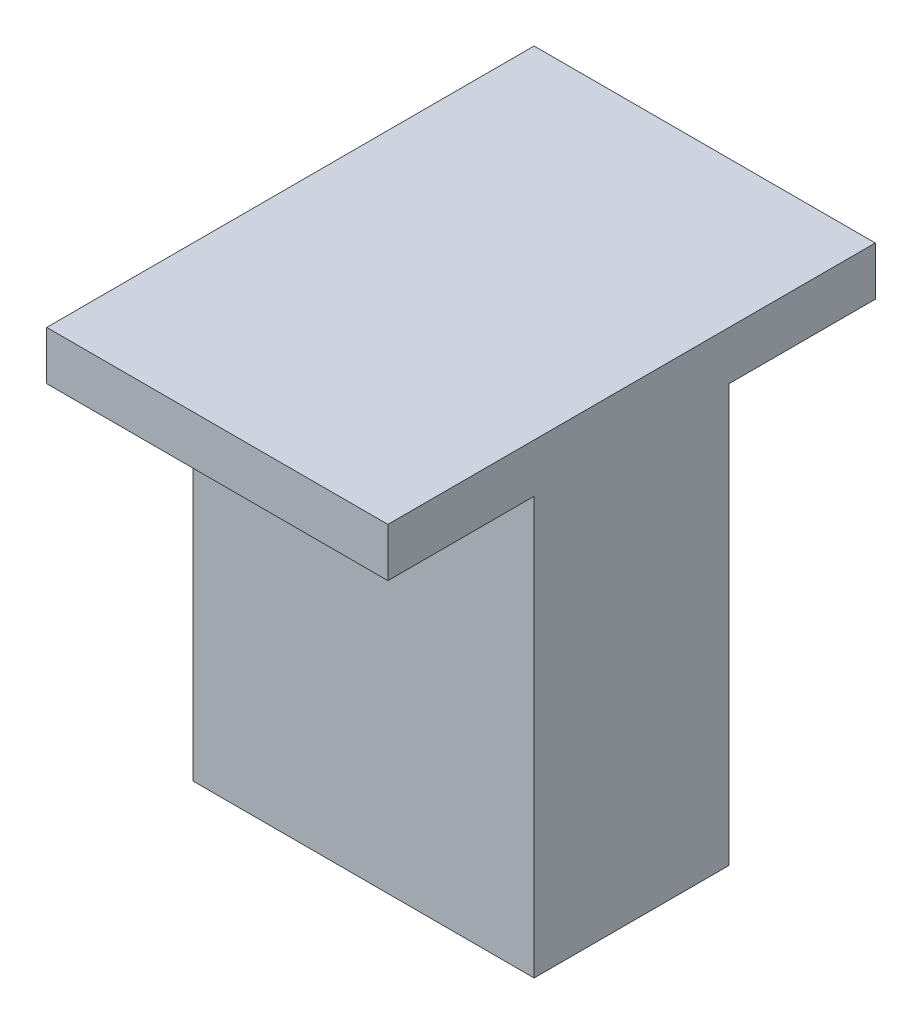
SolidWorks part; units mm, degrees
material "Pine"
ref_plane "Front Plane" through (0, 0, 0) normal (0, 0, 1) x (1, 0, 0)
ref_plane "Top Plane" through (0, 0, 0) normal (0, 1, 0) x (1, 0, 0)
ref_plane "Right Plane" through (0, 0, 0) normal (1, 0, 0) x (0, 0, -1)
sketch "Sketch2" plane through (0, 0, 0) normal (0, 1, 0) x (1, 0, 0)
  line L1 (-17.5, 10) -> (17.5, 10)
  line L2 (-17.5, 10) -> (-17.5, -10)
  line L3 (-17.5, -10) -> (17.5, -10)
  line L4 (17.5, 10) -> (17.5, -10)
  line L5 (-17.5, 10) -> (17.5, -10) construction
  line L6 (-17.5, -10) -> (17.5, 10) construction
  point P0 (0, 0)
extrude "Boss-Extrude1" add sketch "Sketch2" along normal blind 47.8
sketch "Sketch3" plane through (0, 47.8, 0) normal (0, 1, 0) x (1, 0, 0)
  line L1 (-17.5, -25) -> (17.5, -25)
  line L2 (-17.5, -25) -> (-17.5, 25)
  line L3 (-17.5, 25) -> (17.5, 25)
  line L4 (17.5, -25) -> (17.5, 25)
  line L5 (-17.5, -25) -> (17.5, 25) construction
  line L6 (-17.5, 25) -> (17.5, -25) construction
  point P0 (0, 0)
  dimension "D1" = 35
  dimension "D2" = 50
extrude "Boss-Extrude2" add sketch "Sketch3" against normal blind 5
